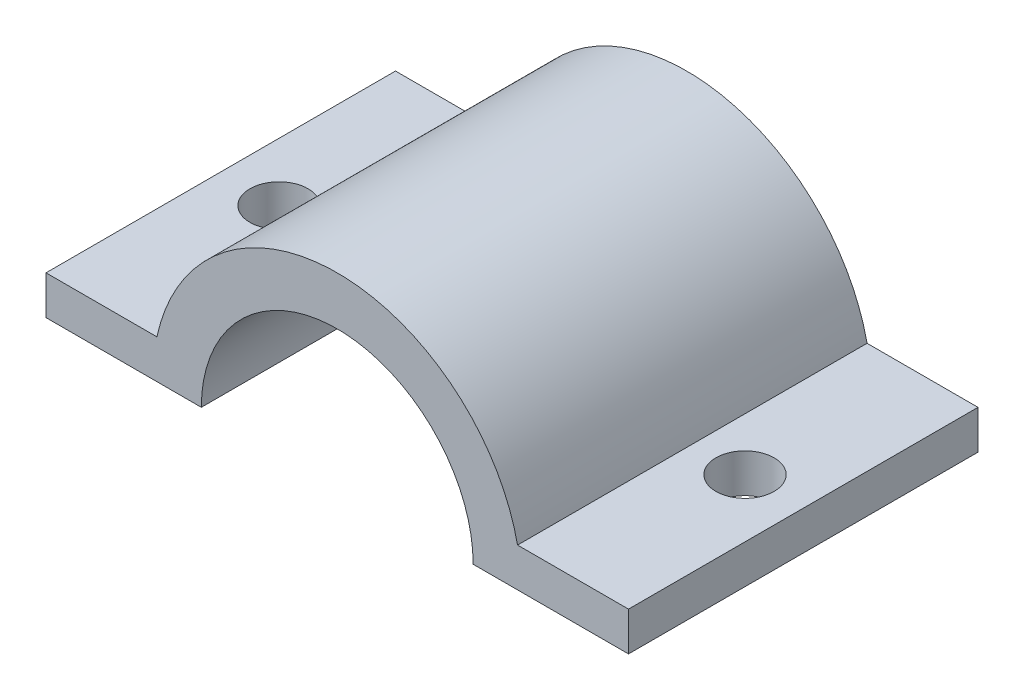
SolidWorks part; units mm, degrees
material "Plástico personalizado"
ref_plane "Plano frontal" through (0, 0, 0) normal (0, 0, 1) x (1, 0, 0)
ref_plane "Plano superior" through (0, 0, 0) normal (0, 1, 0) x (1, 0, 0)
ref_plane "Plano direito" through (0, 0, 0) normal (1, 0, 0) x (0, 0, -1)
sketch "Esboço1" plane through (0, 0, 0) normal (0, 0, 1) x (1, 0, 0)
  line L0 (10.0871, 2) -> (15.8, 2)
  line L1 (-14.2, 0) -> (-6.2, 0)
  line L2 (-14.2, 0) -> (-14.2, 2)
  line L3 (-14.2, 2) -> (-8.4871, 2)
  line L4 (15.8, 0) -> (15.8, 2)
  line L5 (7.8, 0) -> (15.8, 0)
  arc A0 (10.0871, 2) -> (-8.4871, 2) centre (0.8, 0) ccw
  arc A1 (7.8, 0) -> (-6.2, 0) centre (0.8, 0) ccw
  point P4 (0, 0)
  dimension "D3" = 19
  dimension "D4" = 14
  dimension "D1" = 30
  dimension "D2" = 2
extrude "Ressalto-extrusão1" add sketch "Esboço1" along normal blind 18
sketch "Esboço2" plane through (0, 2, 0) normal (0, 1, 0) x (1, 0, 0)
  line L2 (15.8, -18) -> (15.8, 0) construction
  line L3 (-8.4871, 0) -> (-14.2, 0) construction
  line L4 (-14.2, -18) -> (-14.2, 0) construction
  circle A0 centre (12.8, -9) radius 1.5
  circle A1 centre (-11.2, -9) radius 1.5
  dimension "D1" = 3
  dimension "D2" = 3
  dimension "D3" = 9
  dimension "D4" = 3
extrude "Corte-extrusão1" cut sketch "Esboço2" against normal blind 17
